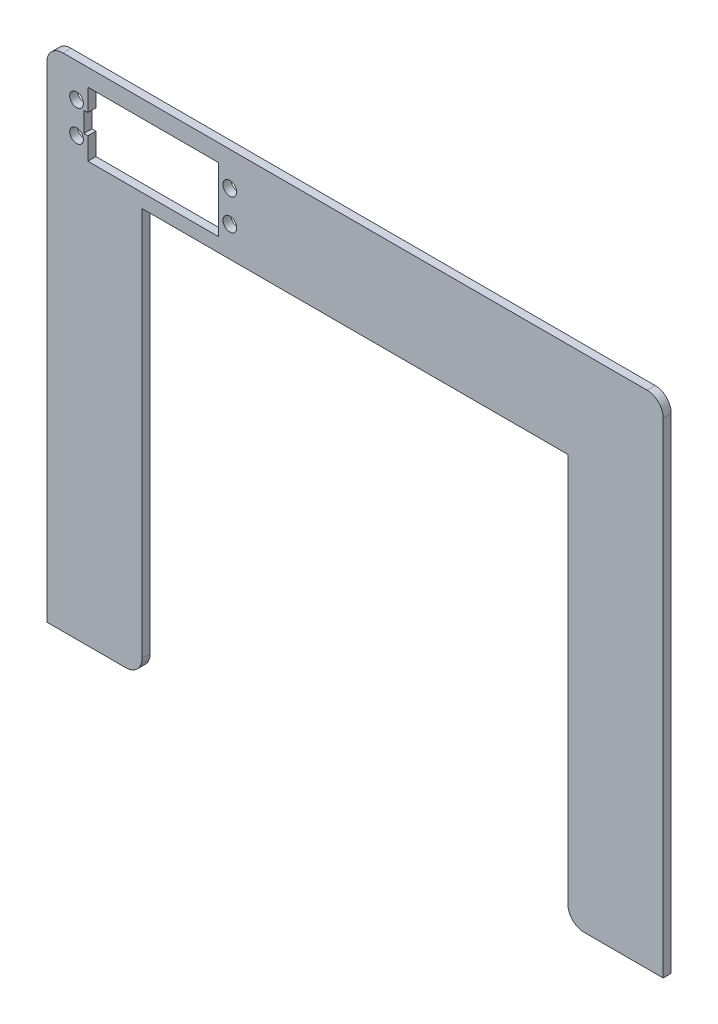
SolidWorks part; units mm, degrees
ref_plane "Front Plane" through (0, 0, 0) normal (0, 0, 1) x (1, 0, 0)
ref_plane "Top Plane" through (0, 0, 0) normal (0, 1, 0) x (1, 0, 0)
ref_plane "Right Plane" through (0, 0, 0) normal (1, 0, 0) x (0, 0, -1)
sketch "Sketch1" plane through (0, 0, 0) normal (0, 0, 1) x (1, 0, 0)
  line L0 (67.0433, -78.881) -> (67.0433, 48.881)
  line L1 (97.0433, -78.881) -> (67.0433, -78.881)
  line L2 (97.0433, -78.881) -> (97.0433, 78.881)
  line L3 (97.0433, 78.881) -> (-97.0433, 78.881)
  line L4 (-97.0433, -78.881) -> (-97.0433, 78.881)
  line L5 (97.0433, -78.881) -> (-97.0433, 78.881) construction
  line L6 (97.0433, 78.881) -> (-97.0433, -78.881) construction
  line L7 (67.0433, 48.881) -> (-67.0433, 48.881)
  line L8 (-67.0433, 48.881) -> (-67.0433, -78.881)
  line L9 (-67.0433, -78.881) -> (-97.0433, -78.881)
  line L10 (0, 0) -> (0, 78.881) construction
  point P0 (0, 0)
  dimension "D1" = 134.0866
  dimension "D2" = 127.762
  dimension "D3" = 30
  dimension "D4" = 30
extrude "Boss-Extrude1" add sketch "Sketch1" along normal blind 2.54
sketch "Sketch2" plane through (0, 0, 2.54) normal (0, 0, 1) x (1, 0, 0)
  line L0 (-72.0433, 73.4555) -> (-72.0433, 53.2625) construction
  line L1 (-42.9603, 73.4555) -> (-84.1083, 73.4555)
  line L2 (-42.9603, 73.4555) -> (-42.9603, 63.359)
  line L3 (-42.9603, 53.2625) -> (-84.1083, 53.2625)
  line L4 (-84.1083, 73.4555) -> (-84.1083, 53.2625)
  line L5 (-42.9603, 73.4555) -> (-84.1083, 53.2625) construction
  line L6 (-42.9603, 53.2625) -> (-84.1083, 73.4555) construction
  line L8 (-84.1083, 63.359) -> (-42.9603, 63.359) construction
  line L9 (-97.0433, -78.881) -> (-67.0433, -78.881) construction
  line L10 (-63.5343, 73.4555) -> (-63.5343, 53.2625) construction
  line L11 (-87.6643, 68.2485) -> (-87.6643, 58.4695) construction
  line L12 (-39.4043, 58.4695) -> (-39.4043, 68.2485) construction
  line L13 (-87.6643, 68.2485) -> (-39.4043, 68.2485) construction
  line L14 (-67.0433, -78.881) -> (-67.0433, 48.881) construction
  line L18 (-42.9603, 63.359) -> (-42.9603, 53.2625)
  circle A0 centre (-87.6643, 68.2485) radius 2.159
  circle A1 centre (-87.6643, 58.4695) radius 2.159
  circle A2 centre (-39.4043, 68.2485) radius 2.159
  circle A3 centre (-39.4043, 58.4695) radius 2.159
  point P0 (-63.5343, 63.359)
  dimension "D6" = 4.318
  dimension "D1" = 41.148
  dimension "D2" = 20.193
  dimension "D3" = 12.065
  dimension "D4" = 142.24
  dimension "D5" = 48.26
  dimension "D7" = 9.779
  dimension "D8" = 5
extrude "Cut-Extrude1" cut sketch "Sketch2" against normal blind 2.54
fillet "Fillet1" radius 5.08 4 edges at (67.0433, -78.881, 1.27) (-67.0433, -78.881, 1.27) (97.0433, 78.881, 1.27) (-97.0433, 78.881, 1.27)
sketch "Sketch3" plane through (0, 0, 2.54) normal (0, 0, 1) x (1, 0, 0)
  line L0 (-84.1083, 73.4555) -> (-84.1083, 53.2625) construction
  line L1 (-82.8383, 60.184) -> (-85.3783, 60.184)
  line L2 (-82.8383, 60.184) -> (-82.8383, 66.534)
  line L3 (-82.8383, 66.534) -> (-85.3783, 66.534)
  line L4 (-85.3783, 60.184) -> (-85.3783, 66.534)
  line L5 (-82.8383, 60.184) -> (-85.3783, 66.534) construction
  line L6 (-82.8383, 66.534) -> (-85.3783, 60.184) construction
  point P0 (-84.1083, 63.359)
  dimension "D1" = 2.54
  dimension "D2" = 6.35
extrude "Cut-Extrude4" cut sketch "Sketch3" against normal through all
